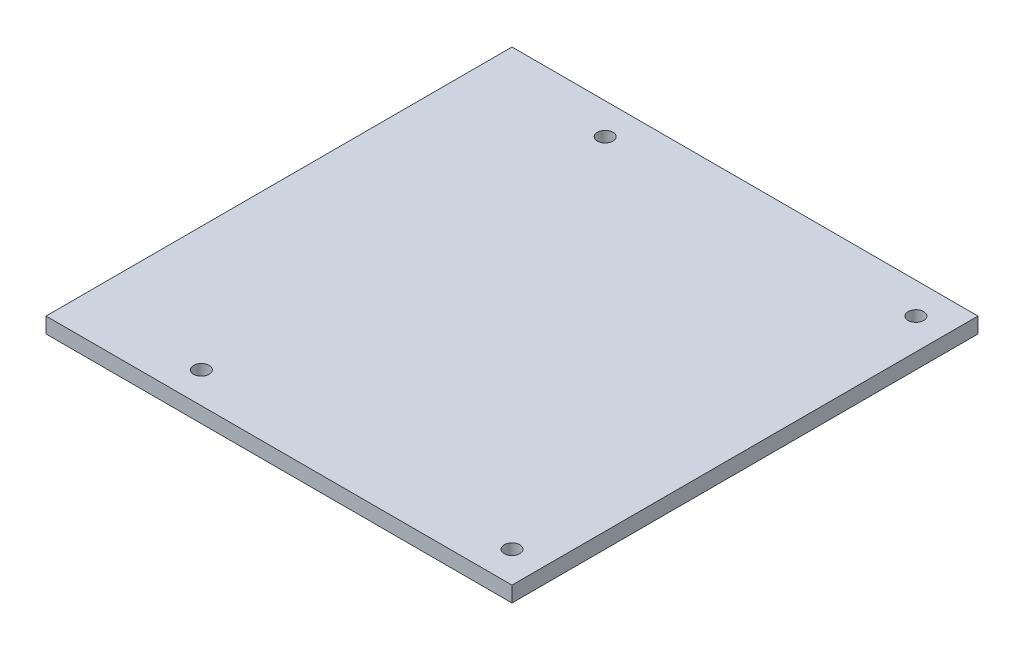
SolidWorks part; units mm, degrees
ref_plane "Alzado" through (0, 0, 0) normal (0, 0, 1) x (1, 0, 0)
ref_plane "Planta" through (0, 0, 0) normal (0, 1, 0) x (1, 0, 0)
ref_plane "Vista lateral" through (0, 0, 0) normal (1, 0, 0) x (0, 0, -1)
sketch "Croquis1" plane through (0, 0, 0) normal (0, 1, 0) x (1, 0, 0)
  line L0 (-82.7689, -42.4559) -> (67.2311, -42.4559)
  line L1 (-82.7689, 32.5441) -> (67.2311, 32.5441)
  line L2 (-82.7689, 32.5441) -> (-82.7689, -117.4559)
  line L3 (-82.7689, -117.4559) -> (67.2311, -117.4559)
  line L4 (67.2311, 32.5441) -> (67.2311, -117.4559)
  circle A0 centre (-42.7689, 22.5441) radius 2.5
  circle A1 centre (57.2311, 22.5441) radius 2.5
  circle A2 centre (57.2311, -107.4559) radius 2.5
  circle A3 centre (-42.7689, -107.4559) radius 2.5
  dimension "D3" = 5
  dimension "D4" = 5
  dimension "D1" = 150
  dimension "D2" = 150
  dimension "D5" = 10
  dimension "D6" = 10
  dimension "D7" = 100
  dimension "D8" = 10
extrude "Saliente-Extruir1" add sketch "Croquis1" along normal blind 5 contours L4 L0 L2 L3 A2 A3 | L4 L1 L2 L0 A1 A0
